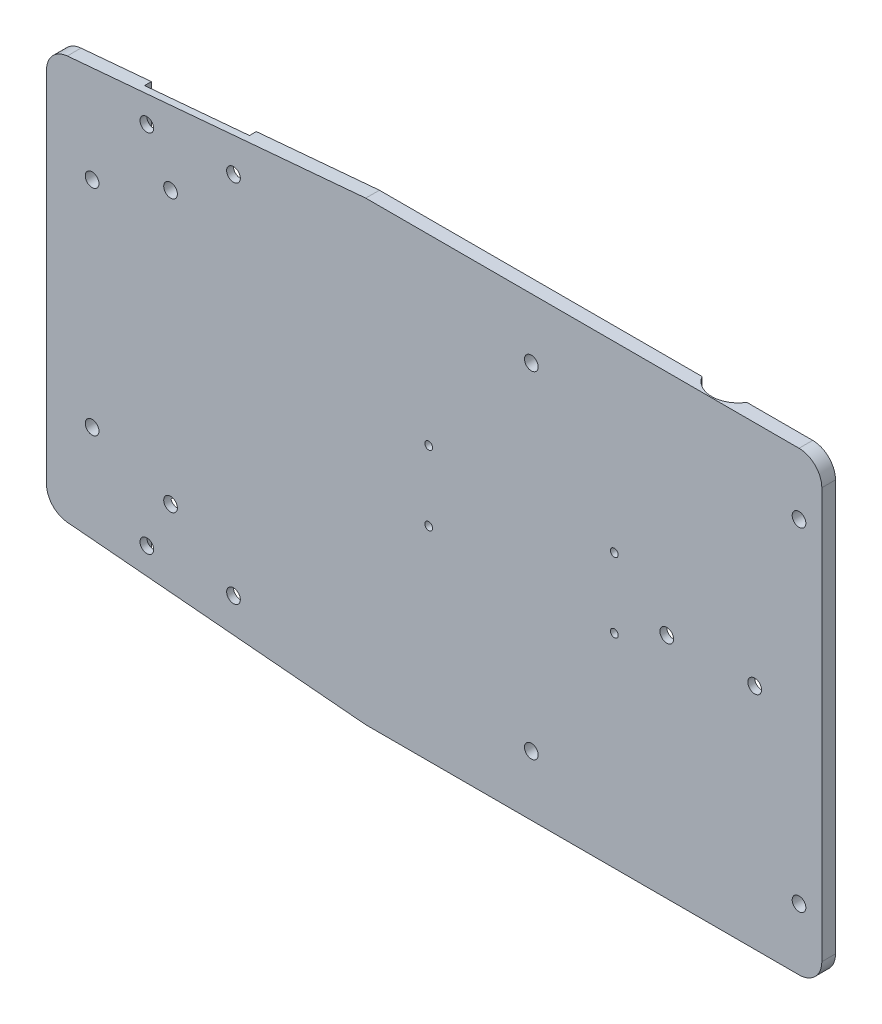
SolidWorks part; units mm, degrees
ref_plane "Ön Düzlem" through (0, 0, 0) normal (0, 0, 1) x (1, 0, 0)
ref_plane "Üst Düzlem" through (0, 0, 0) normal (0, 1, 0) x (1, 0, 0)
ref_plane "Sağ Düzlem" through (0, 0, 0) normal (1, 0, 0) x (0, 0, -1)
sketch "Sketch1" plane through (0, 0, 0) normal (0, 0, 1) x (1, 0, 0)
  line L0 (-65.4358, 44.2751) -> (0, 50)
  line L1 (0, 50) -> (95, 50)
  line L2 (-70, 39.2941) -> (-70, -39.2941)
  line L3 (0, -50) -> (95, -50)
  line L4 (100, 45) -> (100, -45)
  line L5 (-85.108, 42.554) -> (100, -50) construction
  line L6 (-85.108, -42.554) -> (100, 50) construction
  line L7 (-65.4358, -44.2751) -> (0, -50)
  arc A0 (100, -45) -> (95, -50) centre (95, -45) cw
  arc A1 (100, 45) -> (95, 50) centre (95, 45) ccw
  arc A2 (-65.4358, -44.2751) -> (-70, -39.2941) centre (-65, -39.2941) cw
  arc A3 (-65.4358, 44.2751) -> (-70, 39.2941) centre (-65, 39.2941) ccw
  point P0 (0, 0)
  dimension "D1" = 5
  dimension "D2" = 100
  dimension "D3" = 5
  dimension "D4" = 5
  dimension "D5" = 170
  dimension "D6" = 70
  dimension "D7" = 50
  dimension "D8" = 100
extrude "Boss-Extrude1" add sketch "Sketch1" along normal blind 3
sketch "Sketch2" plane through (0, 0, 3) normal (0, 0, 1) x (1, 0, 0)
  line L0 (95, 50) -> (0, 50) construction
  line L1 (0, -50) -> (95, -50) construction
  line L3 (-70, 39.2941) -> (-70, -39.2941) construction
  circle A4 centre (-48, -40) radius 1.5
  circle A5 centre (-29, -40) radius 1.5
  circle A6 centre (-48, 40) radius 1.5
  circle A7 centre (-29, 40) radius 1.5
  dimension "D1" = 10
  dimension "D6" = 19
  dimension "D7" = 10
  dimension "D8" = 22
extrude "Cut-Extrude1" cut sketch "Sketch2" against normal blind 10
ref_plane "Plane1" through (0, 32.5, 0) normal (0, 1, 0) x (1, 0, 0)
sketch "Sketch6" plane through (0, 50, 0) normal (0, 1, 0) x (1, 0, 0)
  line L12 (-27, 0) -> (-27, -1.5)
  line L13 (-27, -1.5) -> (-50, -1.5)
  line L14 (-50, 0) -> (-27, 0)
  line L15 (-50, -1.5) -> (-50, 0)
  line L16 (-70, -3) -> (-70, 0) construction
  line L18 (0, 0) -> (-65.4358, 0) construction
  line L19 (0, -3) -> (-65.4358, -3) construction
  dimension "D1" = 20
  dimension "D2" = 1.5
  dimension "D4" = 23
extrude "Cut-Extrude2" cut sketch "Sketch6" against normal blind 20
sketch "Sketch7" plane through (0, 0, 0) normal (0, 0, -1) x (-1, 0, 0)
  line L0 (-100, -45) -> (-100, 45) construction
  line L1 (-61, 20.675) -> (5.1, 20.675)
  line L2 (-61, 20.675) -> (-61, -20.675)
  line L3 (-61, -20.675) -> (5.1, -20.675)
  line L4 (5.1, 20.675) -> (5.1, -20.675)
  line L5 (-61, 20.675) -> (5.1, -20.675) construction
  line L6 (-61, -20.675) -> (5.1, 20.675) construction
  point P0 (-11, 0)
  point P10 (-27.95, 0)
  dimension "D1" = 66.1
  dimension "D2" = 41.35
  dimension "D3" = 39
extrude "Cut-Extrude3" cut sketch "Sketch7" against normal blind 1.5
sketch "Sketch9" plane through (0, 0, 0) normal (0, 0, -1) x (-1, 0, 0)
  line L0 (5.1, 20.675) -> (-61, 20.675) construction
  line L5 (-61, 20.675) -> (-61, -20.675) construction
  circle A0 centre (-54.5, 9.925) radius 0.85
  circle A1 centre (-54.5, -5.375) radius 0.85
  circle A2 centre (-13.8, 9.925) radius 0.85
  circle A3 centre (-13.8, -5.375) radius 0.85
  dimension "D1" = 1.7
  dimension "D2" = 1.7
  dimension "D6" = 40.7
  dimension "D3" = 10.75
  dimension "D4" = 15.3
  dimension "D5" = 6.5
  dimension "D7" = 15.3
extrude "Cut-Extrude4" cut sketch "Sketch9" against normal blind 6.5
sketch "Sketch10" plane through (0, 0, 0) normal (0, 0, -1) x (-1, 0, 0)
  line L0 (5.1, -20.675) -> (5.1, 20.675) construction
  line L1 (7.1, 21.5) -> (50.1, 21.5)
  line L2 (7.1, 21.5) -> (7.1, -21.5)
  line L3 (7.1, -21.5) -> (50.1, -21.5)
  line L4 (50.1, 21.5) -> (50.1, -21.5)
  line L5 (7.1, 21.5) -> (50.1, -21.5) construction
  line L6 (7.1, -21.5) -> (50.1, 21.5) construction
  point P0 (28.6, 0)
  dimension "D1" = 43
  dimension "D2" = 43
  dimension "D3" = 2
extrude "Cut-Extrude5" cut sketch "Sketch10" against normal blind 1.5
mirror "Mirror1" about plane through (0, 0, 0) normal (0, 1, 0) of "Cut-Extrude2"
sketch "Sketch17" plane through (0, 0, 0) normal (0, 0, -1) x (-1, 0, 0)
  line L0 (0, -50) -> (-95, -50) construction
  line L1 (-95, 50) -> (0, 50) construction
  circle A0 centre (-36.3095, -36.85) radius 1.5
  circle A1 centre (-36.3095, 36.85) radius 1.5
  dimension "D3" = 3
  dimension "D4" = 3
  dimension "D1" = 13.15
  dimension "D2" = 13.15
sketch "Sketch18" plane through (0, 0, 0) normal (0, 0, -1) x (-1, 0, 0)
  line L0 (-100, -45) -> (-100, 45) construction
  line L1 (-95, 50) -> (0, 50) construction
  line L2 (0, -50) -> (-95, -50) construction
  line L3 (70, 39.2941) -> (70, -39.2941) construction
  circle A0 centre (-95, -36.5) radius 1.5
  circle A1 centre (-95, 36.5) radius 1.5
  circle A2 centre (60, -23.5) radius 1.5
  circle A3 centre (60, 23.5) radius 1.5
  dimension "D2" = 3
  dimension "D5" = 3
  dimension "D6" = 3
  dimension "D1" = 5
  dimension "D3" = 13.5
  dimension "D4" = 13.5
  dimension "D7" = 10
  dimension "D8" = 10
  dimension "D9" = 26.5
  dimension "D10" = 26.5
sketch "Sketch19" plane through (0, 0, 0) normal (0, 0, -1) x (-1, 0, 0)
  line L0 (-100, -45) -> (-100, 45) construction
  line L1 (-90, 20.8228) -> (-62, 20.8228)
  line L2 (-90, 20.8228) -> (-90, -20.8228)
  line L3 (-90, -20.8228) -> (-62, -20.8228)
  line L4 (-62, 20.8228) -> (-62, -20.8228)
  line L5 (-90, 20.8228) -> (-62, -20.8228) construction
  line L6 (-90, -20.8228) -> (-62, 20.8228) construction
  point P0 (-76, 0)
  dimension "D1" = 38
  dimension "D2" = 28
extrude "Cut-Extrude11" cut sketch "Sketch17" against normal blind 30.5
extrude "Cut-Extrude12" cut sketch "Sketch18" against normal blind 30.5
extrude "Cut-Extrude13" cut sketch "Sketch19" against normal blind 1.5
sketch "Sketch20" plane through (0, 0, 1.5) normal (0, 0, -1) x (-1, 0, 0)
  line L0 (-62, -20.8228) -> (-62, 20.8228) construction
  circle A0 centre (-66, 0) radius 1.5
  circle A1 centre (-85.28, 0) radius 1.5
  point P6 (-62, 0)
  dimension "D1" = 3
  dimension "D2" = 19.28
  dimension "D3" = 4
extrude "Cut-Extrude14" cut sketch "Sketch20" against normal blind 1.5
sketch "Sketch21" plane through (0, 0, 3) normal (0, 0, 1) x (1, 0, 0)
  line L0 (-70, 39.2941) -> (-70, -39.2941) construction
  circle A0 centre (-42.8, 30.1) radius 1.5
  circle A1 centre (-42.8, -29.5) radius 1.5
  dimension "D1" = 3
  dimension "D2" = 3
  dimension "D3" = 59.6
  dimension "D5" = 27.2
  dimension "D4" = 29.5
extrude "Cut-Extrude15" cut sketch "Sketch21" against normal blind 10
ref_plane "Plane2" through (75.64, 0, 0) normal (1, 0, 0) x (0, 0, -1)
ref_plane "Plane3" through (0, 50, 0) normal (0, 1, 0) x (1, 0, 0)
sketch "Sketch23" plane through (0, 50, 0) normal (0, 1, 0) x (1, 0, 0)
  line L0 (75.64, -1.65) -> (75.64, 1.65) construction
  line L1 (95, -3) -> (0, -3) construction
  circle A0 centre (75.64, 3) radius 5.75
  point P4 (0, 0)
  dimension "D1" = 11.5
  dimension "D2" = 6
extrude "Cut-Extrude16" cut sketch "Sketch23" against normal blind 4
mirror "Mirror2" about plane through (0, 0, 0) normal (0, 1, 0) of "Cut-Extrude16"
